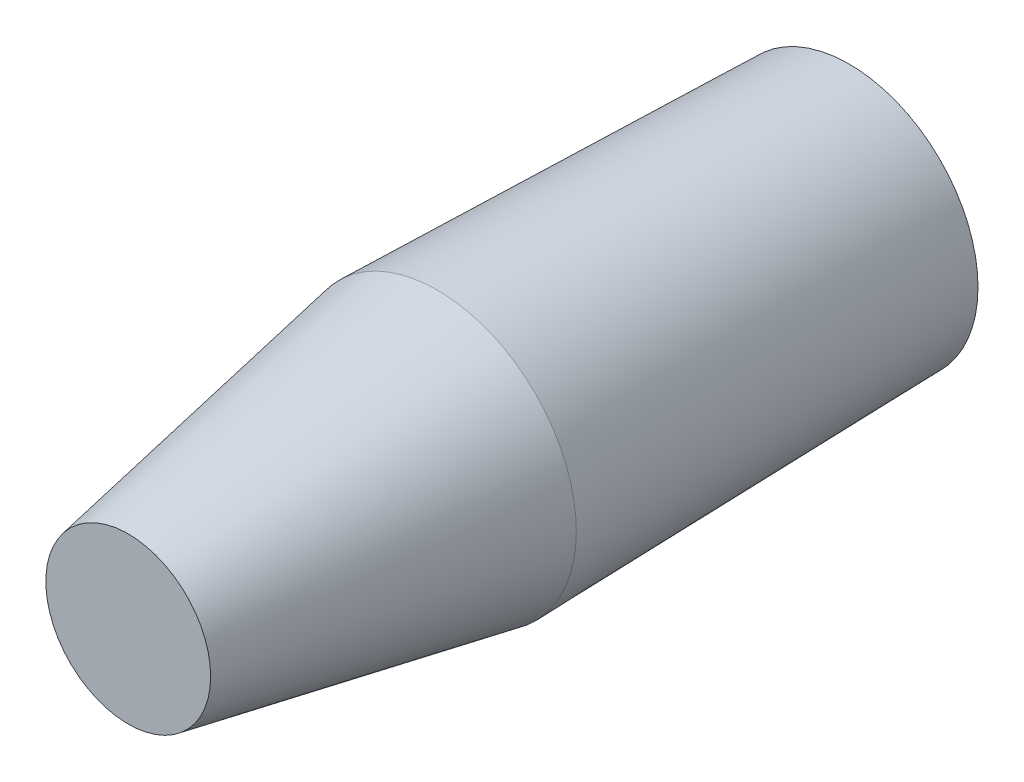
SolidWorks part; units mm, degrees
ref_plane "Front Plane" through (0, 0, 0) normal (0, 0, 1) x (1, 0, 0)
ref_plane "Top Plane" through (0, 0, 0) normal (0, 1, 0) x (1, 0, 0)
ref_plane "Right Plane" through (0, 0, 0) normal (1, 0, 0) x (0, 0, -1)
sketch "Sketch1" plane through (0, 0, 0) normal (0, 0, 1) x (1, 0, 0)
  circle A0 centre (0, 0) radius 25
ref_plane "Plane1" through (0, 0, 80) normal (0, 0, 1) x (1, 0, 0)
sketch "Sketch2" plane through (0, 0, 80) normal (0, 0, 1) x (1, 0, 0)
  circle A0 centre (0, 0) radius 27
ref_plane "Plane2" through (0, 0, 140) normal (0, 0, 1) x (1, 0, 0)
sketch "Sketch3" plane through (0, 0, 140) normal (0, 0, 1) x (1, 0, 0)
  circle A0 centre (0, 0) radius 16
loft "Loft1" add profiles "Sketch1", "Sketch2"
loft "Loft2" add profiles "Sketch3" section edge at (27, 0, 80) section "Sketch3"
